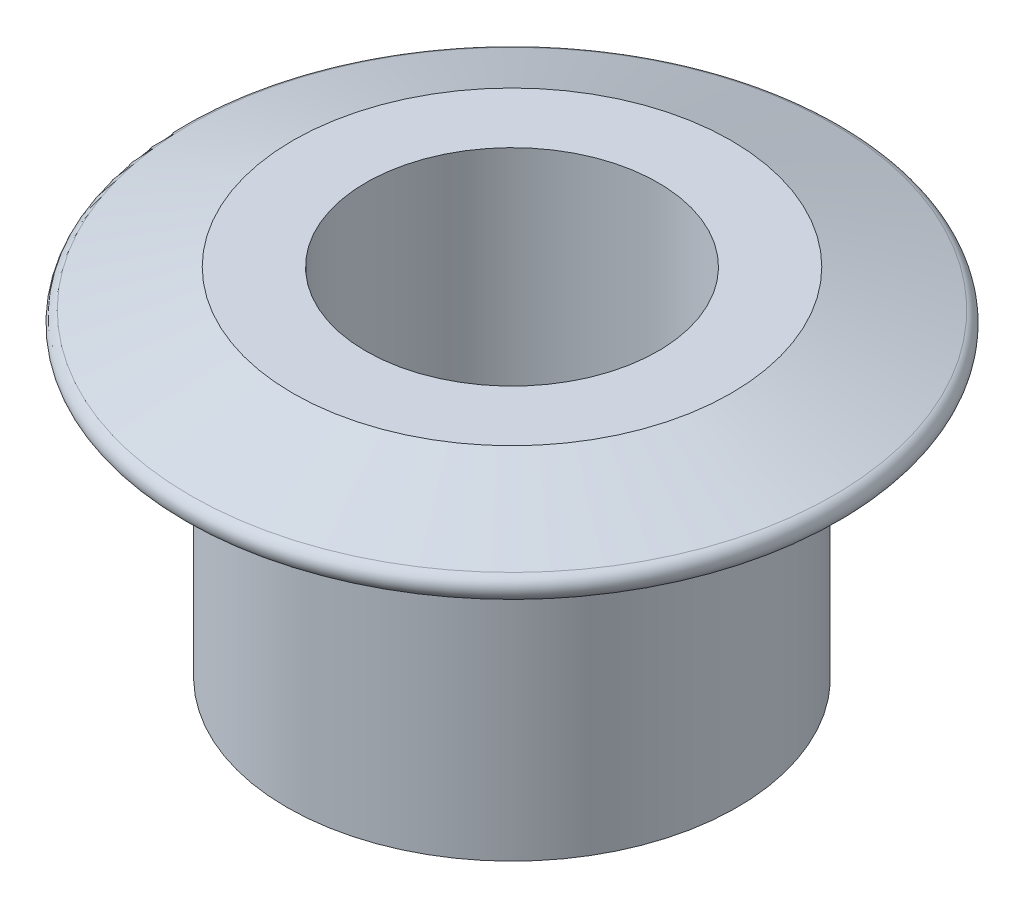
SolidWorks part; units mm, degrees
ref_plane "Front Plane" through (0, 0, 0) normal (0, 0, 1) x (1, 0, 0)
ref_plane "Top Plane" through (0, 0, 0) normal (0, 1, 0) x (1, 0, 0)
ref_plane "Right Plane" through (0, 0, 0) normal (1, 0, 0) x (0, 0, -1)
sketch "Sketch1" plane through (0, 0, 0) normal (0, 0, 1) x (1, 0, 0)
  line L0 (0, 25.0607) -> (0, -29.5399) construction
  line L1 (0, 5) -> (18, 5)
  line L2 (18, 5) -> (31.76, 0)
  line L3 (31.76, 0) -> (18.5, 0)
  line L4 (18.5, 0) -> (18.5, -24.21)
  line L5 (18.5, -24.21) -> (0, -24.21)
  line L6 (0, 5) -> (0, -24.21)
  dimension "D1" = 18.5
  dimension "D2" = 31.76
  dimension "D3" = 29.21
  dimension "D4" = 5
revolve "Revolve1" add sketch "Sketch1" angle 360 about L0
sketch "Sketch2" plane through (0, 5, 0) normal (0, 1, 0) x (1, 0, 0)
  circle A0 centre (0, 0) radius 12
extrude "Cut-Extrude1" cut sketch "Sketch2" against normal up to next
fillet "Fillet1" radius 1 1 edges at (0, 0, 31.76)
